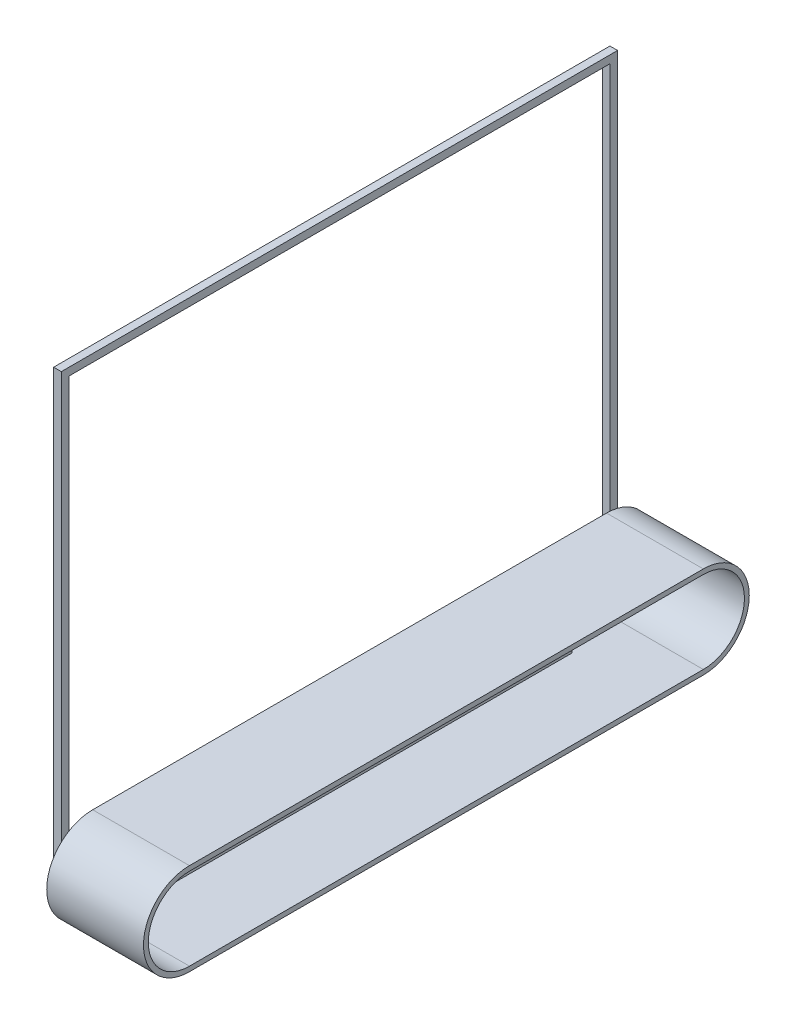
SolidWorks part; units mm, degrees
ref_plane "Front Plane" through (0, 0, 0) normal (0, 0, 1) x (1, 0, 0)
ref_plane "Top Plane" through (0, 0, 0) normal (0, 1, 0) x (1, 0, 0)
ref_plane "Right Plane" through (0, 0, 0) normal (1, 0, 0) x (0, 0, -1)
sketch "Sketch1" plane through (0, 0, 0) normal (1, 0, 0) x (0, 0, -1)
  line L0 (-559.125, -472.0175) -> (-559.125, 472.0175)
  line L2 (-575, -487.8925) -> (-575, 487.8925)
  line L3 (-575, 487.8925) -> (575, 487.8925)
  line L4 (575, -487.8925) -> (575, 487.8925)
  line L5 (-575, -487.8925) -> (575, 487.8925) construction
  line L6 (-575, 487.8925) -> (575, -487.8925) construction
  line L7 (-559.125, 472.0175) -> (559.125, 472.0175)
  line L8 (559.125, -472.0175) -> (559.125, 472.0175)
  line L9 (-575, -487.8925) -> (-559.125, -487.8925)
  line L10 (559.125, -487.8925) -> (575, -487.8925)
  line L11 (-559.125, -487.8925) -> (559.125, -487.8925)
  line L12 (-559.125, -472.0175) -> (559.125, -472.0175)
  line L14 (559.125, -487.8925) -> (559.125, 472.0175) construction
  line L15 (-559.125, -487.8925) -> (-559.125, 472.0175) construction
  point P0 (0, 0)
  point P7 (0, 0)
  dimension "D1" = 1150
  dimension "D2" = 975.785
  dimension "D4" = 15.875
  dimension "D3" = 15.875
extrude "Boss-Extrude1" add sketch "Sketch1" along normal blind 15.875
sketch "Sketch2" plane through (15.875, 0, 0) normal (1, 0, 0) x (0, 0, -1)
  line L1 (-425, -487.8925) -> (-409.125, -487.8925)
  line L2 (-425, -487.8925) -> (-425, -472.0175)
  line L3 (-425, -472.0175) -> (-409.125, -472.0175)
  line L4 (-409.125, -487.8925) -> (-409.125, -472.0175)
  line L10 (-559.125, -472.0175) -> (559.125, -472.0175) construction
  line L11 (-575, 487.8925) -> (-575, -487.8925) construction
  line L12 (0, 8.7312) -> (0, -8.7312) construction
  line L13 (425, -472.0175) -> (409.125, -472.0175)
  line L14 (409.125, -487.8925) -> (409.125, -472.0175)
  line L15 (425, -487.8925) -> (409.125, -487.8925)
  line L16 (425, -487.8925) -> (425, -472.0175)
  dimension "D1" = 15.875
  dimension "D3" = 150
  dimension "D4" = 15.875
extrude "Boss-Extrude2" add sketch "Sketch2" along normal blind 55.785
sketch "Sketch3" plane through (0, 0, 425) normal (0, 0, 1) x (1, 0, 0)
  line L7 (15.875, 487.8925) -> (15.875, -487.8925) construction
  line L8 (55.875, -472.0175) -> (71.75, -472.0175)
  line L9 (55.875, -472.0175) -> (55.875, -487.8925)
  line L10 (55.875, -487.8925) -> (71.75, -487.8925)
  line L11 (71.75, -472.0175) -> (71.75, -487.8925)
  line L12 (71.66, -472.0175) -> (15.875, -472.0175) construction
  dimension "40" = 40
  dimension "D2" = 15.875
  dimension "D5" = 15.875
extrude "Boss-Extrude3" add sketch "Sketch3" against normal up to surface (850 mm away) up to face at (43.7675, -479.955, -425)
sketch "Sketch4" plane through (15.875, 0, 0) normal (1, 0, 0) x (0, 0, -1)
  line L0 (425, -487.8925) -> (-425, -487.8925) construction
  line L1 (425, -487.8925) -> (-425, -487.8925)
  line L2 (-531.125, -402.8925) -> (531.125, -402.8925) construction
  line L3 (-531.125, -317.8925) -> (531.125, -317.8925)
  line L4 (-531.125, -487.8925) -> (531.125, -487.8925)
  arc A0 (-531.125, -317.8925) -> (-531.125, -487.8925) centre (-531.125, -402.8925) ccw
  arc A1 (531.125, -487.8925) -> (531.125, -317.8925) centre (531.125, -402.8925) ccw
  point P4 (0, -402.8925)
  dimension "D1" = 85
  dimension "D2" = 1062.25
extrude "Extrude-Thin2" add sketch "Sketch4" along normal blind 200 from offset 21 thin contours L4 A1 L3 A0 thin type one direction wall 10
sketch "Sketch5" plane through (15.875, 0, 0) normal (1, 0, 0) x (0, 0, -1)
  line L0 (-575, 487.8925) -> (-575, -487.8925) construction
  line L1 (-575, -352.8925) -> (-559.125, -352.8925)
  line L2 (-575, -352.8925) -> (-575, -452.8925)
  line L3 (-575, -452.8925) -> (-559.125, -452.8925)
  line L4 (-559.125, -352.8925) -> (-559.125, -452.8925)
  line L5 (-559.125, 472.0175) -> (-559.125, -472.0175) construction
  line L6 (-531.125, -317.8925) -> (-531.125, -487.8925) construction
  line L7 (-575, -487.8925) -> (-425, -487.8925) construction
  arc A4 (-531.125, -317.8925) -> (-531.125, -487.8925) centre (-531.125, -402.8925) ccw construction
  point P19 (-575, -402.8925)
  point P20 (-531.125, -402.8925)
  dimension "D1" = 100
extrude "Boss-Extrude4" add sketch "Sketch5" along normal blind 120
sketch "Sketch7" plane through (135.875, 0, 0) normal (1, 0, 0) x (0, 0, -1)
  line L2 (-559.125, -352.8925) -> (-505.125, -352.8925)
  line L3 (-559.125, -352.8925) -> (-559.125, -452.8925)
  line L4 (-559.125, -452.8925) -> (-505.125, -452.8925)
  line L5 (-505.125, -352.8925) -> (-505.125, -452.8925)
  circle A0 centre (-531.125, -402.8925) radius 15
  point P2 (-559.125, -402.8925)
  dimension "D1" = 30
  dimension "D2" = 28
  dimension "D3" = 54
extrude "Boss-Extrude5" add sketch "Sketch7" against normal blind 20
sketch "Sketch9" plane through (71.75, 0, 0) normal (1, 0, 0) x (0, 0, -1)
  line L0 (-425, -472.0175) -> (-312.5414, -472.0175)
  line L1 (425, -472.0175) -> (-425, -472.0175) construction
  line L2 (-312.5414, -472.0175) -> (-559.125, -436.8569)
  line L3 (-559.125, -436.8569) -> (-559.125, -452.8925)
  line L4 (-559.125, -452.8925) -> (-425, -472.0175)
  line L5 (-559.125, 472.0175) -> (-559.125, -352.8925) construction
  line L6 (-575, -452.8925) -> (-505.125, -452.8925) construction
  dimension "D1" = 15.875
extrude "Boss-Extrude6" add sketch "Sketch9" against normal up to surface (15.875 mm away) up to face at (55.875, -479.955, 0)
sketch "Sketch11" plane through (0, 0, 559.125) normal (0, 0, -1) x (-1, 0, 0)
  line L0 (-115.875, -352.8925) -> (-115.875, -452.8925) construction
  line L1 (-115.875, -437.0175) -> (-15.875, -437.0175)
  line L2 (-115.875, -437.0175) -> (-115.875, -368.7675)
  line L3 (-115.875, -368.7675) -> (-15.875, -368.7675)
  line L4 (-15.875, -437.0175) -> (-15.875, -368.7675)
  line L5 (-15.875, 472.0175) -> (-15.875, -352.8925) construction
  line L6 (-115.875, -352.8925) -> (-15.875, -352.8925) construction
  line L7 (-55.875, -452.8925) -> (-15.875, -452.8925) construction
  dimension "D1" = 15.875
  dimension "D2" = 15.875
extrude "Cut-Extrude1" cut sketch "Sketch11" against normal blind 20
